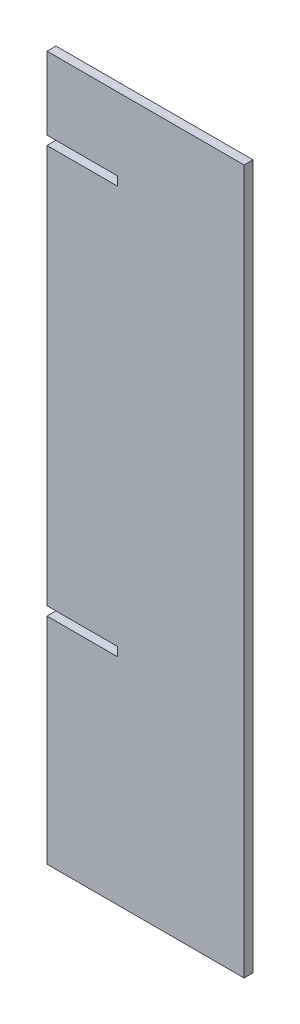
SolidWorks part; units mm, degrees
material "FiberBoard"
ref_plane "Front Plane" through (0, 0, 0) normal (0, 0, 1) x (1, 0, 0)
ref_plane "Top Plane" through (0, 0, 0) normal (0, 1, 0) x (1, 0, 0)
ref_plane "Right Plane" through (0, 0, 0) normal (1, 0, 0) x (0, 0, -1)
sketch "Sketch1" plane through (0, 0, 0) normal (0, 0, 1) x (1, 0, 0)
  line L1 (-35, 125) -> (35, 125)
  line L2 (-35, 125) -> (-35, -125)
  line L3 (-35, -125) -> (35, -125)
  line L4 (35, 125) -> (35, -125)
  line L5 (-35, 125) -> (35, -125) construction
  line L6 (-35, -125) -> (35, 125) construction
  point P0 (0, 0)
  dimension "D1" = 70
  dimension "D2" = 250
extrude "Boss-Extrude1" add sketch "Sketch1" along normal blind 3.175
sketch "Sketch2" plane through (0, 0, 3.175) normal (0, 0, 1) x (1, 0, 0)
  line L0 (-35, 125) -> (-35, -125) construction
  line L1 (-35, 99.18) -> (-10, 99.18)
  line L2 (-35, 99.18) -> (-35, 96.005)
  line L3 (-35, 96.005) -> (-10, 96.005)
  line L4 (-10, 99.18) -> (-10, 96.005)
  line L5 (35, -125) -> (35, 125) construction
  line L6 (35, 99.18) -> (10, 99.18) construction
  line L7 (35, 99.18) -> (35, 96.005) construction
  line L8 (35, 96.005) -> (10, 96.005) construction
  line L9 (10, 99.18) -> (10, 96.005) construction
  line L10 (-35, -125) -> (35, -125) construction
  line L11 (-35, -45.52) -> (-10, -45.52)
  line L12 (-35, -45.52) -> (-35, -48.695)
  line L13 (-35, -48.695) -> (-10, -48.695)
  line L14 (-10, -45.52) -> (-10, -48.695)
  line L15 (35, -45.52) -> (10, -45.52) construction
  line L16 (35, -45.52) -> (35, -48.695) construction
  line L17 (35, -48.695) -> (10, -48.695) construction
  line L18 (10, -45.52) -> (10, -48.695) construction
  dimension "D1" = 25
  dimension "D2" = 3.175
  dimension "D3" = 224.18
  dimension "D4" = 79.48
extrude "Cut-Extrude1" cut sketch "Sketch2" against normal blind 3.175
